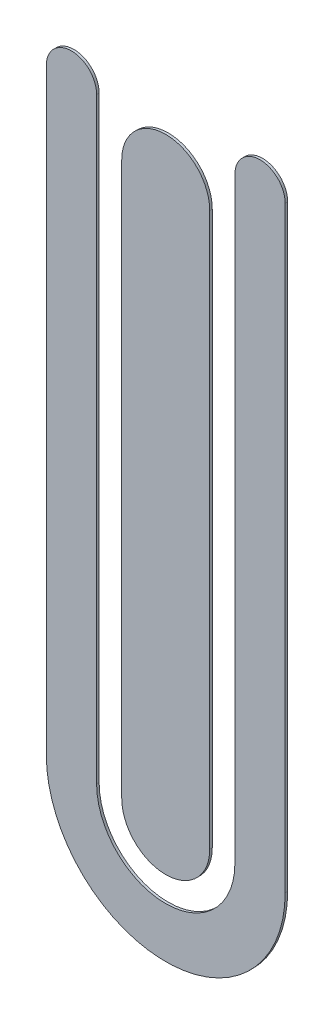
SolidWorks part; units mm, degrees
ref_plane "Ön Düzlem" through (0, 0, 0) normal (0, 0, 1) x (1, 0, 0)
ref_plane "Üst Düzlem" through (0, 0, 0) normal (0, 1, 0) x (1, 0, 0)
ref_plane "Sağ Düzlem" through (0, 0, 0) normal (1, 0, 0) x (0, 0, -1)
sketch "Çizim1" plane through (0, 0, 0) normal (0, 0, 1) x (1, 0, 0)
  line L0 (0, 22) -> (0, -22) construction
  line L1 (3.5, 22) -> (3.5, -22)
  line L2 (-3.5, 22) -> (-3.5, -22)
  line L3 (7.5, 25.5) -> (7.5, -22) construction
  line L4 (9.5, 25.5) -> (9.5, -22)
  line L5 (5.5, 25.5) -> (5.5, -22)
  line L6 (-7.5, 25.5) -> (-7.5, -22) construction
  line L7 (-5.5, 25.5) -> (-5.5, -22)
  line L8 (-9.5, 25.5) -> (-9.5, -22)
  line L9 (0, 25.5) -> (9.1857, 25.5) construction
  line L10 (0, 25.5) -> (-8.4269, 25.5) construction
  arc A0 (3.5, 22) -> (-3.5, 22) centre (0, 22) ccw
  arc A1 (-3.5, -22) -> (3.5, -22) centre (0, -22) ccw
  arc A2 (9.5, 25.5) -> (5.5, 25.5) centre (7.5, 25.5) ccw
  arc A4 (-5.5, 25.5) -> (-9.5, 25.5) centre (-7.5, 25.5) ccw
  arc A6 (-7.5, -22) -> (7.5, -22) centre (0, -22) ccw construction
  arc A15 (-9.5, -22) -> (9.5, -22) centre (0, -22) ccw
  arc A16 (-5.5, -22) -> (5.5, -22) centre (0, -22) ccw
  point P2 (0, 0)
  point P7 (7.5, 0)
  point P15 (-7.5, 0)
  point P25 (0, -29.5)
  dimension "D2" = 44
  dimension "D8" = 7.5
  dimension "D7" = 4
  dimension "D1" = 7
  dimension "D3" = 4
  dimension "D4" = 4
  dimension "D5" = 7.5
  dimension "D6" = 7.5
extrude "Yükseklik-Ekstrüzyon1" add sketch "Çizim1" along normal blind 0.2
